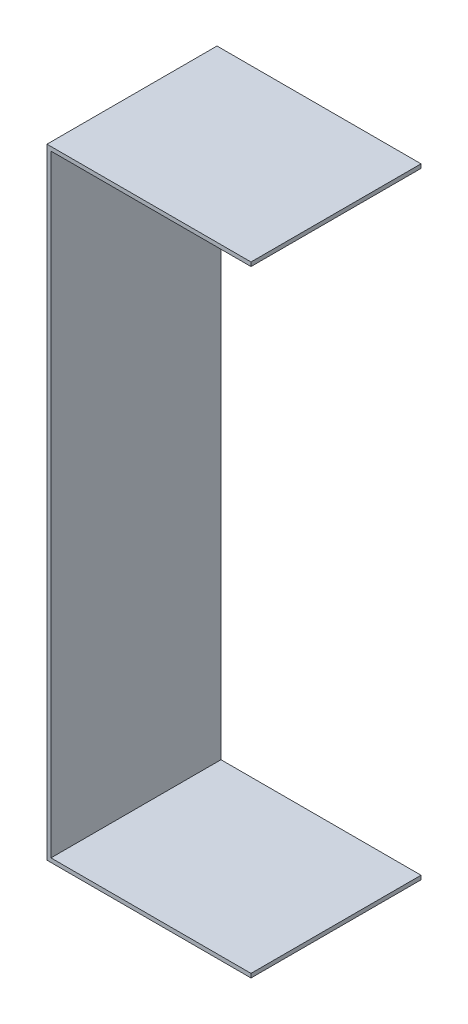
SolidWorks part; units mm, degrees
ref_plane "Front Plane" through (0, 0, 0) normal (0, 0, 1) x (1, 0, 0)
ref_plane "Top Plane" through (0, 0, 0) normal (0, 1, 0) x (1, 0, 0)
ref_plane "Right Plane" through (0, 0, 0) normal (1, 0, 0) x (0, 0, -1)
sketch "Sketch1" plane through (0, 0, 0) normal (0, 0, 1) x (1, 0, 0)
  line L0 (0, 0) -> (0, 306)
  line L1 (0, 306) -> (100, 306)
  line L2 (0, 0) -> (100, 0)
  line L3 (-2, -2) -> (100, -2)
  line L4 (-2, -2) -> (-2, 308)
  line L5 (-2, 308) -> (100, 308)
  line L6 (100, 308) -> (100, 306)
  line L7 (100, 0) -> (100, -2)
  dimension "D1" = 306
  dimension "D2" = 100
  dimension "D3" = 100
  dimension "D4" = 2
extrude "Boss-Extrude1" add sketch "Sketch1" along normal blind 85
